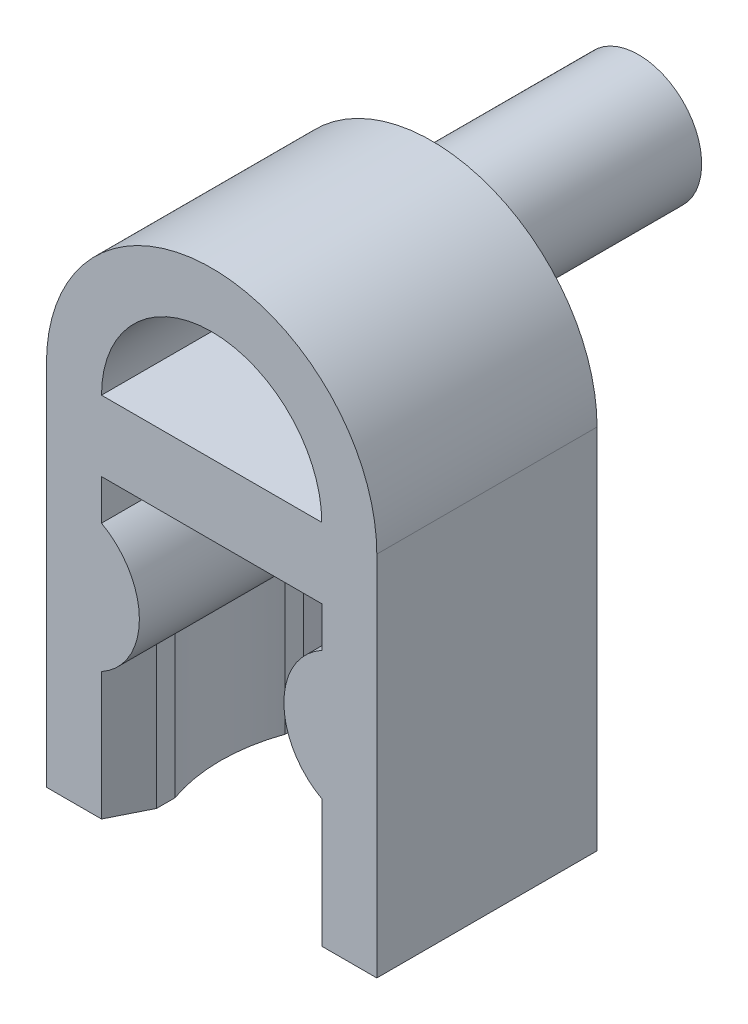
SolidWorks part; units mm, degrees
ref_plane "前视基准面" through (0, 0, 0) normal (0, 0, 1) x (1, 0, 0)
ref_plane "上视基准面" through (0, 0, 0) normal (0, 1, 0) x (1, 0, 0)
ref_plane "右视基准面" through (0, 0, 0) normal (1, 0, 0) x (0, 0, -1)
sketch "草图1" plane through (0, 0, 0) normal (0, 0, 1) x (1, 0, 0)
  line L0 (4.5, 0) -> (4.5, -10)
  line L1 (-4.5, 0) -> (-4.5, -10)
  line L2 (-3, -10) -> (-3, -6.52)
  line L3 (-4.5, -10) -> (-3, -10)
  line L4 (4.5, -10) -> (3, -10)
  line L5 (3, -10) -> (3, -6.52)
  line L6 (-3, -3.02) -> (-3, -1.92)
  line L7 (-3, -1.92) -> (3, -1.92)
  line L8 (3, -1.92) -> (3, -3.02)
  arc A0 (4.5, 0) -> (-4.5, 0) centre (0, 0) ccw
  arc A1 (-3, -3.02) -> (-3, -6.52) centre (-3.9682, -4.77) cw
  arc A2 (3, -3.02) -> (3, -6.52) centre (3.9682, -4.77) ccw
  point P16 (0, 4.5)
  dimension "D1" = 9
  dimension "D7" = 2
  dimension "D10" = 2
  dimension "D2" = 10
  dimension "D3" = 10
  dimension "D4" = 1.5
  dimension "D5" = 1.5
  dimension "D6" = 6.42
  dimension "D8" = 3.5
  dimension "D9" = 3.5
  dimension "D11" = 1.1
  dimension "D12" = 1.1
extrude "凸台-拉伸1" add sketch "草图1" along normal blind 6
sketch "草图2" plane through (0, 0, 6) normal (0, 0, 1) x (1, 0, 0)
  line L0 (3, 0) -> (-3, 0)
  arc A0 (3, 0) -> (-3, 0) centre (0, 0) ccw
  dimension "D1" = 3
  dimension "D2" = 6
extrude "切除-拉伸1" cut sketch "草图2" against normal blind 4
sketch "草图3" plane through (0, 0, 0) normal (0, 0, -1) x (-1, 0, 0)
  circle A0 centre (0, 2) radius 1.72
  dimension "D1" = 3.44
  dimension "D2" = 2
extrude "凸台-拉伸2" add sketch "草图3" along normal blind 5.63
sketch "草图4" plane through (0, -10, 0) normal (0, -1, 0) x (1, 0, 0)
  line L0 (-3, 0) -> (-3, 6)
  line L1 (2.5, 5) -> (2.5, 4.5)
  line L2 (2.5, 1) -> (2.5, 1.5)
  line L3 (2.5, 1) -> (3, 0)
  line L4 (0, 0) -> (0, 6.5234) construction
  line L5 (3, 0) -> (3, 6)
  line L6 (-2.5, 5) -> (-3, 6)
  line L7 (2.5, 5) -> (3, 6)
  line L8 (-2.5, 1) -> (-3, 0)
  line L10 (-2.5, 1) -> (-2.5, 1.5)
  line L11 (-2.5, 5) -> (-2.5, 4.5)
  arc A0 (-2.5, 4.5) -> (-2.5, 1.5) centre (1.7426, 3) ccw
  arc A1 (2.5, 4.5) -> (2.5, 1.5) centre (-1.7426, 3) cw
  dimension "D7" = 4.5
  dimension "D1" = 1.5
  dimension "D2" = 1.5
  dimension "D3" = 0.5
  dimension "D4" = 0.5
  dimension "D5" = 0.5
  dimension "D6" = 0.5
extrude "凸台-拉伸5" add sketch "草图4" against normal up to next
